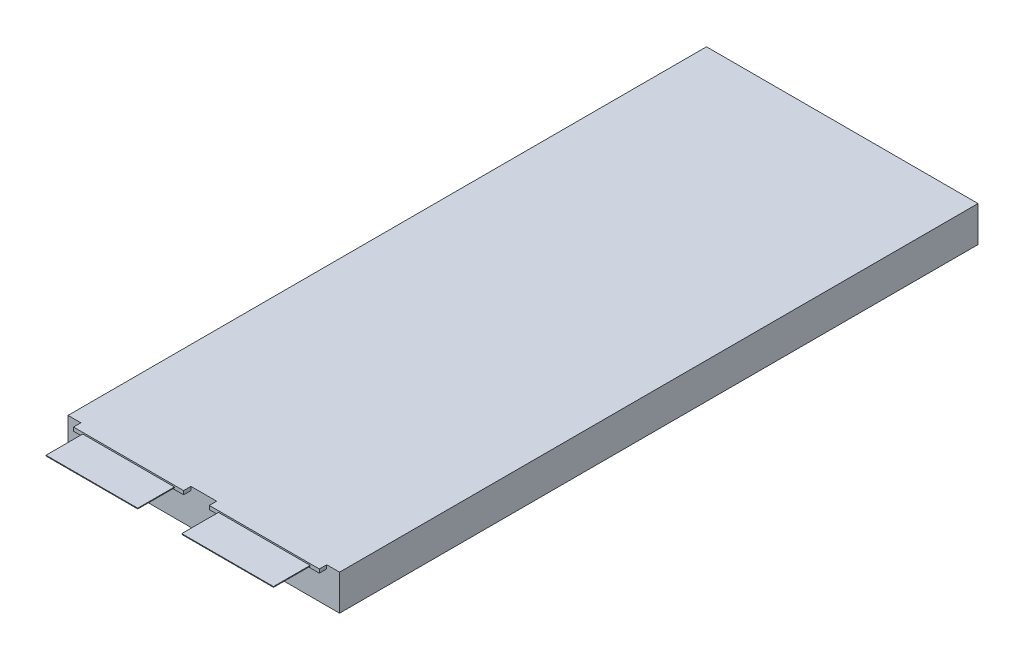
SolidWorks part; units mm, degrees
ref_plane "Płaszczyzna przednia" through (0, 0, 0) normal (0, 0, 1) x (1, 0, 0)
ref_plane "Płaszczyzna górna" through (0, 0, 0) normal (0, 1, 0) x (1, 0, 0)
ref_plane "Płaszczyzna prawa" through (0, 0, 0) normal (1, 0, 0) x (0, 0, -1)
sketch "Szkic1" plane through (0, 0, 0) normal (0, 0, 1) x (1, 0, 0)
  line L1 (0, 0) -> (74, 0)
  line L2 (0, 0) -> (0, -9.7)
  line L3 (0, -9.7) -> (74, -9.7)
  line L4 (74, 0) -> (74, -9.7)
  dimension "D1" = 74
  dimension "D2" = 9.7
extrude "Dodanie-wyciągnięcie1" add sketch "Szkic1" along normal blind 174
sketch "Szkic2" plane through (0, 0, 174) normal (0, 0, 1) x (1, 0, 0)
  line L0 (3.5, 0) -> (3.5, -1)
  line L1 (74, 0) -> (0, 0) construction
  line L2 (3.5, -1) -> (33.5, -1)
  line L3 (33.5, -1) -> (33.5, 0)
  line L4 (40.5, 0) -> (40.5, -1)
  line L5 (40.5, -1) -> (70.5, -1)
  line L6 (70.5, -1) -> (70.5, 0)
  line L8 (18.5, 0) -> (3.5, 0)
  line L9 (18.5, 0) -> (33.5, 0)
  line L10 (55.5, 0) -> (40.5, 0)
  line L11 (55.5, 0) -> (70.5, 0)
  point P0 (33.5, -0.5)
  dimension "D1" = 15
  dimension "D2" = 15
  dimension "D3" = 15
  dimension "D4" = 15
  dimension "D5" = 1
  dimension "D6" = 7
  dimension "D7" = 1
  dimension "D8" = 30
  dimension "D9" = 30
  dimension "D10" = 1
  dimension "D11" = 1
extrude "Dodanie-wyciągnięcie2" add sketch "Szkic2" along normal blind 2
sketch "Szkic3" plane through (0, 0, 176) normal (0, 0, 1) x (1, 0, 0)
  line L4 (6, -0.4) -> (31, -0.4)
  line L5 (6, -0.4) -> (6, -0.6)
  line L6 (6, -0.6) -> (31, -0.6)
  line L7 (31, -0.4) -> (31, -0.6)
  line L8 (6, -0.4) -> (31, -0.6) construction
  line L9 (6, -0.6) -> (31, -0.4) construction
  point P6 (18.5, -0.5)
  dimension "D1" = 25
  dimension "D2" = 0.2
sketch "Szkic4" plane through (0, 0, 176) normal (0, 0, 1) x (1, 0, 0)
  line L4 (43, -0.4) -> (68, -0.4)
  line L5 (43, -0.4) -> (43, -0.6)
  line L6 (43, -0.6) -> (68, -0.6)
  line L7 (68, -0.4) -> (68, -0.6)
  line L8 (43, -0.4) -> (68, -0.6) construction
  line L9 (43, -0.6) -> (68, -0.4) construction
  point P6 (55.5, -0.5)
  dimension "D1" = 25
  dimension "D2" = 0.2
extrude "Dodanie-wyciągnięcie3" add sketch "Szkic3" along normal blind 10 contours L4 L7 L6 L5
extrude "Dodanie-wyciągnięcie4" add sketch "Szkic4" along normal blind 10 contours L4 L7 L6 L5
